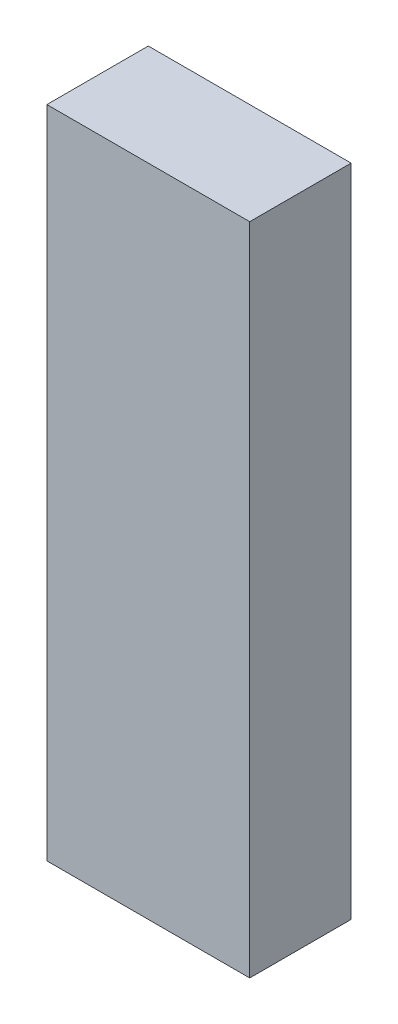
SolidWorks part; units mm, degrees
ref_plane "Front Plane" through (0, 0, 0) normal (0, 0, 1) x (1, 0, 0)
ref_plane "Top Plane" through (0, 0, 0) normal (0, 1, 0) x (1, 0, 0)
ref_plane "Right Plane" through (0, 0, 0) normal (1, 0, 0) x (0, 0, -1)
sketch "Sketch1" plane through (0, 0, 0) normal (0, 0, 1) x (1, 0, 0)
  line L1 (-24, -77.5) -> (24, -77.5)
  line L2 (-24, -77.5) -> (-24, 77.5)
  line L3 (-24, 77.5) -> (24, 77.5)
  line L4 (24, -77.5) -> (24, 77.5)
  line L5 (-24, -77.5) -> (24, 77.5) construction
  line L6 (-24, 77.5) -> (24, -77.5) construction
  point P0 (0, 0)
  dimension "D1" = 155
  dimension "D2" = 48
extrude "Boss-Extrude1" add sketch "Sketch1" along normal blind 24
